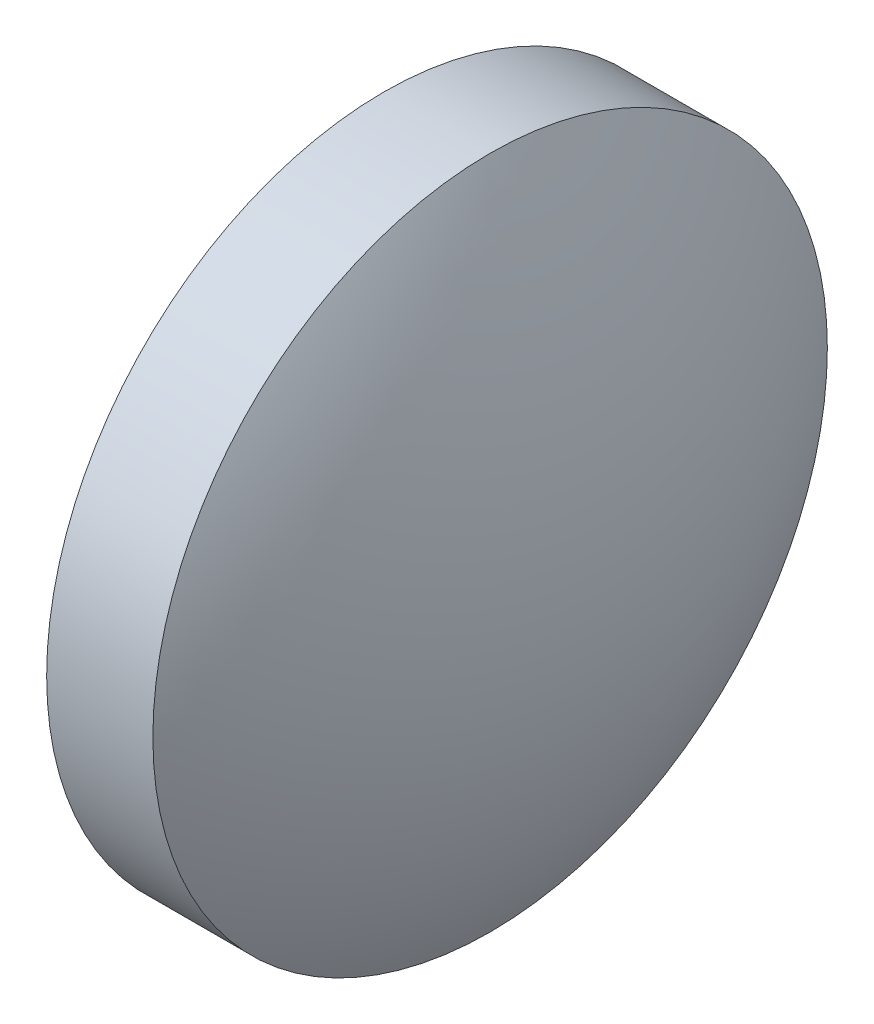
SolidWorks part; units mm, degrees
ref_plane "前视基准面" through (0, 0, 0) normal (0, 0, 1) x (1, 0, 0)
ref_plane "上视基准面" through (0, 0, 0) normal (0, 1, 0) x (1, 0, 0)
ref_plane "右视基准面" through (0, 0, 0) normal (1, 0, 0) x (0, 0, -1)
sketch "草图1" plane through (0, 0, 0) normal (0, 0, 1) x (1, 0, 0)
  line L0 (39.6513, 24.3072) -> (46.737, 24.3072) construction
  line L1 (42.2276, 30.657) -> (44.2276, 30.657)
  line L2 (44.2276, 30.657) -> (44.2276, 17.9574)
  line L3 (44.2276, 17.9574) -> (42.2276, 17.9574)
  line L4 (42.2276, 17.9574) -> (42.2276, 30.657)
  arc A0 (42.2276, 30.657) -> (42.2276, 17.9574) centre (53.3905, 24.3072) ccw
  arc A1 (44.2276, 17.9574) -> (44.2276, 30.657) centre (33.0647, 24.3072) ccw
  dimension "D1" = 2
  dimension "D2" = 12.6996
revolve "旋转1" add sketch "草图1" angle 360 about L0
